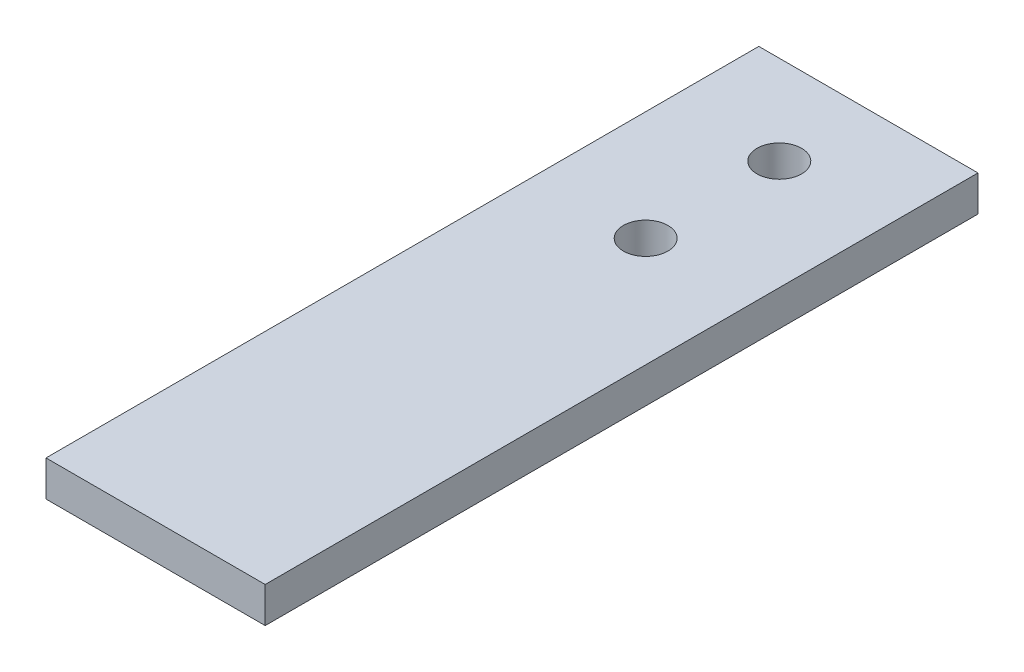
SolidWorks part; units mm, degrees
ref_plane "Front Plane" through (0, 0, 0) normal (0, 0, 1) x (1, 0, 0)
ref_plane "Top Plane" through (0, 0, 0) normal (0, 1, 0) x (1, 0, 0)
ref_plane "Right Plane" through (0, 0, 0) normal (1, 0, 0) x (0, 0, -1)
sketch "Sketch1" plane through (0, 0, 0) normal (0, 1, 0) x (1, 0, 0)
  line L1 (0, 0) -> (31.242, 0)
  line L2 (0, 0) -> (0, 101.6)
  line L3 (0, 101.6) -> (31.242, 101.6)
  line L4 (31.242, 0) -> (31.242, 101.6)
  dimension "D1" = 31.242
  dimension "D2" = 101.6
extrude "Boss-Extrude1" add sketch "Sketch1" along normal blind 5.08
sketch "Sketch2" plane through (0, 0, 0) normal (0, -1, 0) x (1, 0, 0)
  line L0 (31.242, -101.6) -> (0, -101.6) construction
  point P0 (15.621, -88.9)
  point P1 (15.621, -69.85)
  dimension "D1" = 12.7
  dimension "D2" = 19.05
hole_wizard "1/4 (0.25) Diameter Hole1" positions "Sketch3" profile "Sketch4" hole size "1/4" standard "ANSI Inch" end condition through all
sketch "Sketch3" plane through (0, 0, 0) normal (0, -1, 0) x (-1, 0, 0)
  point P0 (-15.621, 69.85)
  point P3 (-15.621, 88.9)
sketch "Sketch4" plane through (15.621, 0, -69.85) normal (1, 0, 0) x (0, 0, -1)
  line L0 (0, 0) -> (0, 5.08)
  line L1 (0, 5.08) -> (3.175, 5.08)
  line L2 (3.175, 5.08) -> (3.175, 0)
  line L5 (3.175, 0) -> (0, 0)
  line L11 (0, -6.35) -> (0, 107.95) construction
  dimension "Thru Hole Dia." = 6.35
  dimension "Thru Hole Depth" = 5.08
